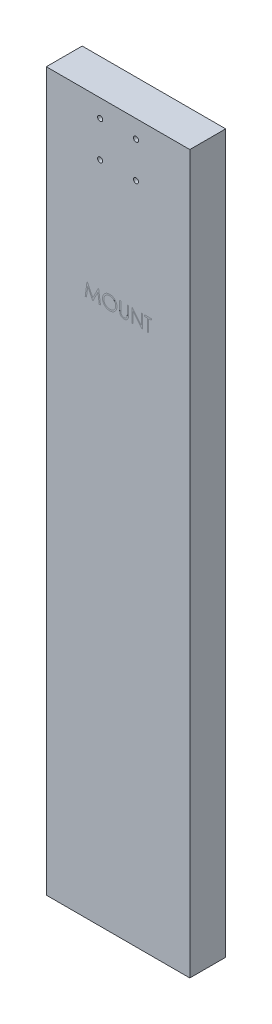
SolidWorks part; units mm, degrees
ref_plane "Front" through (0, 0, 0) normal (0, 0, 1) x (1, 0, 0)
ref_plane "Top" through (0, 0, 0) normal (0, 1, 0) x (1, 0, 0)
ref_plane "Right" through (0, 0, 0) normal (1, 0, 0) x (0, 0, -1)
sketch "Sketch1" plane through (0, 0, 0) normal (0, 0, 1) x (1, 0, 0)
  line L1 (0, 0) -> (200, 0)
  line L2 (0, 0) -> (0, 1000)
  line L3 (0, 1000) -> (200, 1000)
  line L4 (200, 0) -> (200, 1000)
  dimension "D1" = 200
  dimension "D2" = 1000
extrude "Boss-Extrude1" add sketch "Sketch1" along normal blind 50
sketch "Sketch2" plane through (0, 0, 50) normal (0, 0, 1) x (1, 0, 0)
  line L0 (0, 750) -> (200, 750) construction
  line L1 (0, 1000) -> (0, 0) construction
  line L2 (200, 0) -> (200, 1000) construction
  line L3 (200, 1000) -> (0, 1000) construction
  text T0 "MOUNT" font "Century Gothic" height in points 72
  dimension "D1" = 250
extrude "Cut-Extrude1" cut sketch "Sketch2" against normal blind 0.005
sketch "Sketch3" plane through (0, 0, 50) normal (0, 0, 1) x (1, 0, 0)
  line L0 (0, 950) -> (200, 950) construction
  line L1 (0, 1000) -> (0, 0) construction
  line L2 (200, 0) -> (200, 1000) construction
  line L3 (100, 950) -> (100, 975) construction
  line L5 (75, 975) -> (100, 975) construction
  line L6 (200, 1000) -> (0, 1000) construction
  circle A1 centre (75, 975) radius 2.5
  circle A2 centre (75, 925) radius 2.5
  circle A3 centre (125, 925) radius 2.5
  circle A4 centre (125, 975) radius 2.5
  point P11 (0, 0)
  point P21 (100, 950)
  dimension "D1" = 25
  dimension "D3" = 5
  dimension "D2" = 50
  dimension "D4" = 4
hole_wizard "M6 Clearance Hole1" positions "Sketch4" profile "Sketch5" hole size "M6" standard "ANSI Metric" end condition up to next
sketch "Sketch4" plane through (0, 0, 50) normal (0, 0, 1) x (1, 0, 0)
  point P0 (75, 975)
  point P3 (125, 975)
  point P6 (125, 925)
  point P9 (75, 925)
sketch "Sketch5" plane through (75, 975, 50) normal (1, 0, 0) x (0, -1, 0)
  line L0 (0, 0) -> (0, 50)
  line L1 (0, 50) -> (3.5, 50)
  line L2 (3.5, 50) -> (3.5, 0)
  line L5 (3.5, 0) -> (0, 0)
  line L11 (0, -6.35) -> (0, 107.95) construction
  dimension "Thru Hole Dia." = 7
  dimension "Thru Hole Depth" = 50
